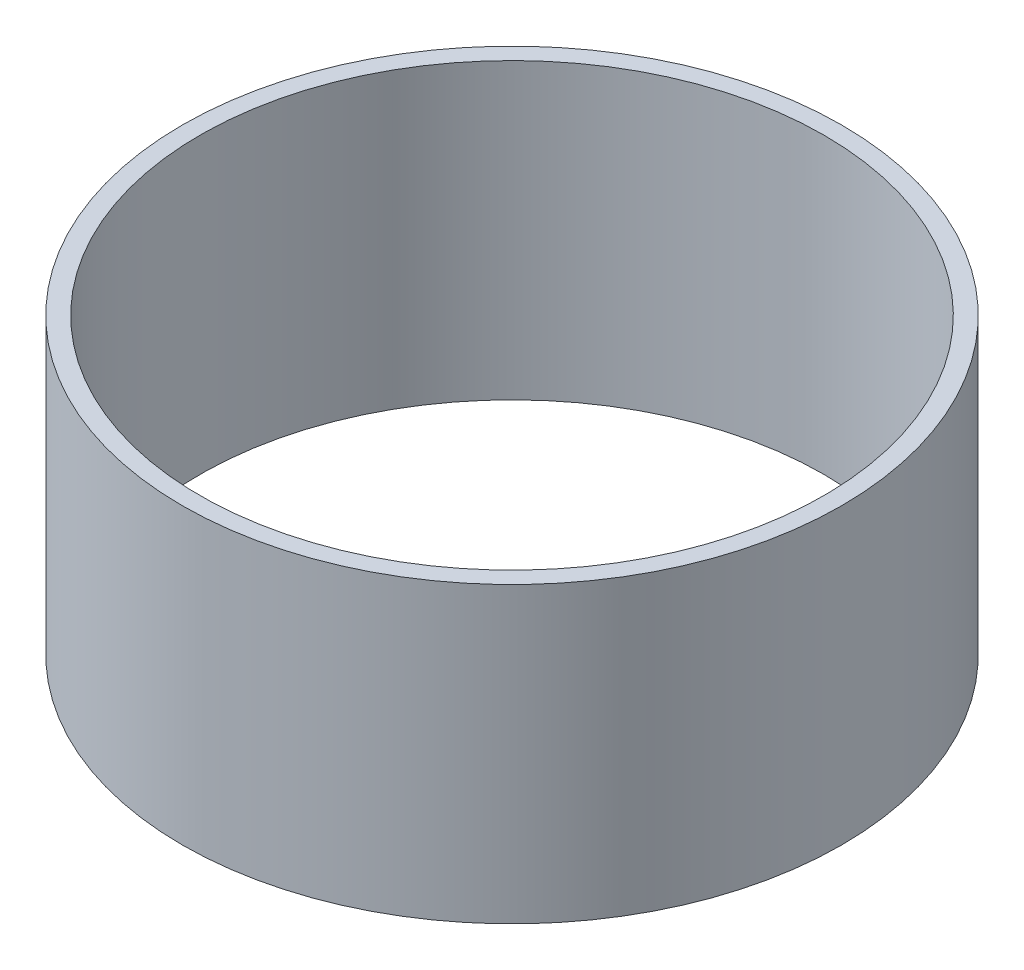
SolidWorks part; units mm, degrees
ref_plane "Front Plane" through (0, 0, 0) normal (0, 0, 1) x (1, 0, 0)
ref_plane "Top Plane" through (0, 0, 0) normal (0, 1, 0) x (1, 0, 0)
ref_plane "Right Plane" through (0, 0, 0) normal (1, 0, 0) x (0, 0, -1)
sketch "Sketch1" plane through (0, 0, 0) normal (0, 0, 1) x (1, 0, 0)
  line L1 (26.9748, 0) -> (28.4988, 0)
  line L2 (26.9748, 0) -> (26.9748, 25.4)
  line L3 (26.9748, 25.4) -> (28.4988, 25.4)
  line L4 (28.4988, 0) -> (28.4988, 25.4)
  dimension "D1" = 28.4988
  dimension "D2" = 1.524
  dimension "D3" = 25.4
  dimension "D4" = 0
ref_axis "Axis1" through (0, -13.97, 0) along (0, 1, 0)
revolve "Revolve1" add sketch "Sketch1" angle 360 about axis through (0, -13.97, 0) along (0, 1, 0)
